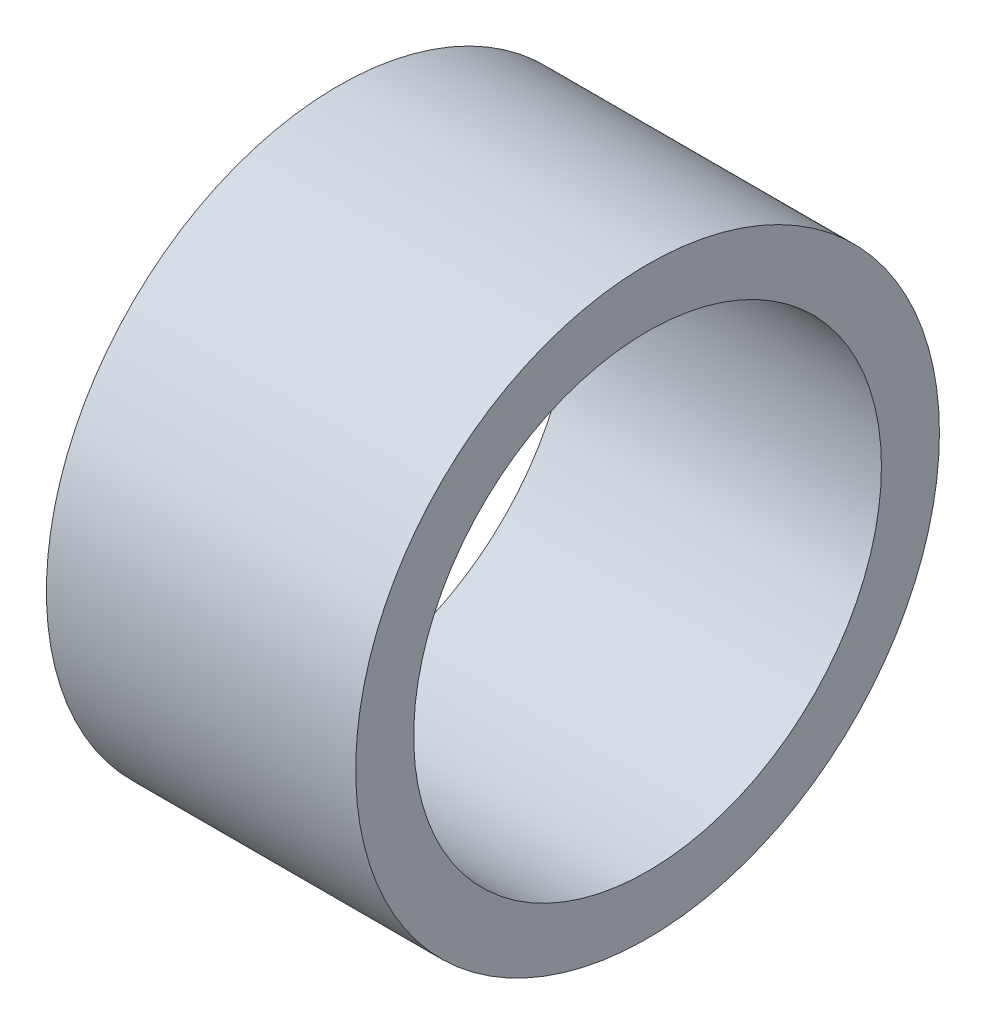
SolidWorks part; units mm, degrees
ref_plane "Front Plane" through (0, 0, 0) normal (0, 0, 1) x (1, 0, 0)
ref_plane "Top Plane" through (0, 0, 0) normal (0, 1, 0) x (1, 0, 0)
ref_plane "Right Plane" through (0, 0, 0) normal (1, 0, 0) x (0, 0, -1)
sketch "Sketch1" plane through (0, 0, 0) normal (1, 0, 0) x (0, 0, -1)
  circle A0 centre (0, 0) radius 7.55
  circle A1 centre (0, 0) radius 6.05
  dimension "D1" = 12.1
  dimension "D2" = 15.1
extrude "Boss-Extrude1" add sketch "Sketch1" along normal blind 8
